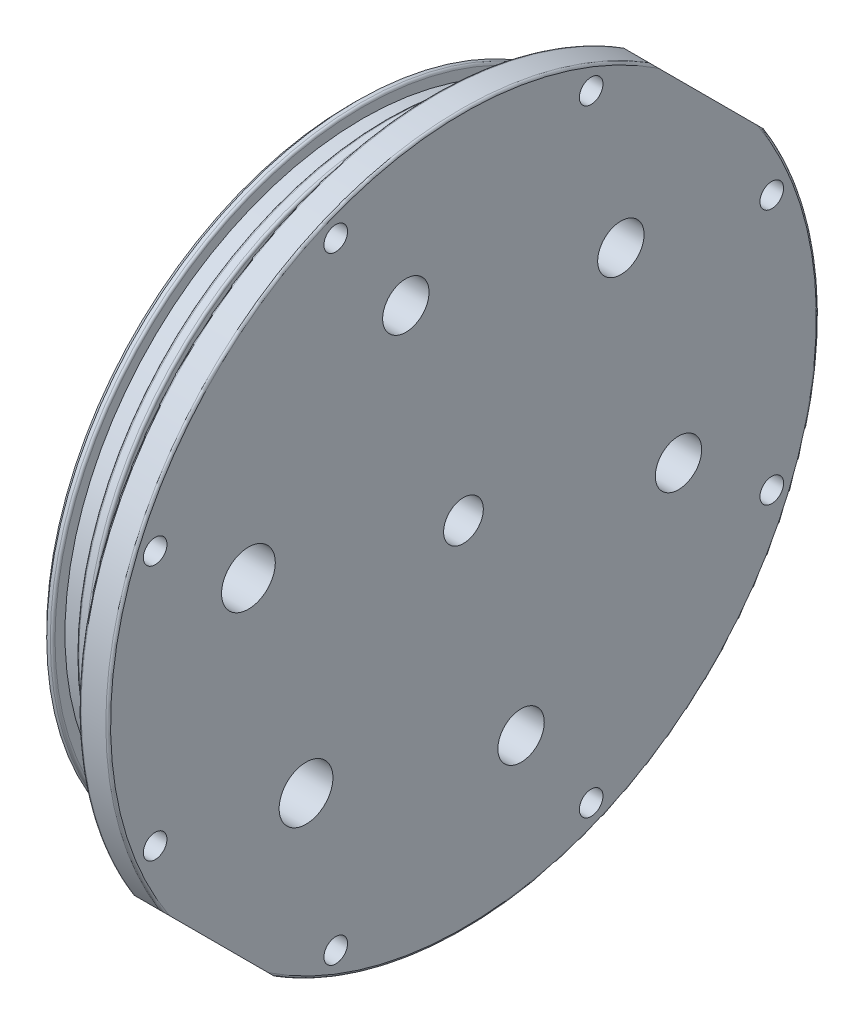
SolidWorks part; units mm, degrees
ref_plane "Front Plane" through (0, 0, 0) normal (0, 0, 1) x (1, 0, 0)
ref_plane "Top Plane" through (0, 0, 0) normal (0, 1, 0) x (1, 0, 0)
ref_plane "Right Plane" through (0, 0, 0) normal (1, 0, 0) x (0, 0, -1)
sketch "Sketch1" plane through (0, 0, 0) normal (0, 0, 1) x (1, 0, 0)
  line L0 (0, 0) -> (0, -58.42) construction
  line L4 (24.13, -58.42) -> (24.13, -76)
  line L5 (24.13, -76) -> (17.8298, -76)
  line L6 (17.8298, -76) -> (17.8298, -66.421)
  line L7 (17.8298, -66.421) -> (0, -66.421) construction
  line L8 (0, -66.294) -> (0, -58.42)
  line L9 (0, -58.42) -> (11.43, -58.42) construction
  line L10 (0, -66.294) -> (2.54, -66.294)
  line L11 (2.54, -66.294) -> (2.54, -63.6575)
  line L12 (2.54, -63.6575) -> (7.6449, -63.6575)
  line L13 (7.6449, -63.6575) -> (7.6449, -66.294)
  line L14 (7.6449, -66.294) -> (10.1849, -66.294)
  line L15 (10.1849, -66.294) -> (10.1849, -63.6575)
  line L16 (10.1849, -63.6575) -> (15.2898, -63.6575)
  line L17 (15.2898, -63.6575) -> (15.2898, -66.294)
  line L18 (15.2898, -66.294) -> (17.8298, -66.294)
  line L19 (17.8298, -66.294) -> (17.8298, -66.421)
  line L20 (0, -66.421) -> (0, -66.294) construction
  line L21 (24.13, -58.42) -> (24.13, 0)
  line L22 (24.13, 0) -> (11.43, 0)
  line L23 (11.43, 0) -> (11.43, -58.42) construction
  line L24 (11.43, -58.42) -> (24.13, -58.42) construction
  line L25 (11.43, 0) -> (0, 0)
  line L26 (0, 0) -> (0, -58.42)
  dimension "CouplerIR" = 58.42
  dimension "CouplerOR" = 76
  dimension "HullR" = 66.421
  dimension "RingSpacing" = 2.54
  dimension "GlandClearanceGap" = 0.254
  dimension "GlandWidth" = 5.1049
  dimension "CouplerHeight" = 24.13
  dimension "BulkheadThickness" = 12.7
  dimension "D1" = 2.7635
revolve "Revolve1" add sketch "Sketch1" angle 360 about L22
chamfer "Chamfer1" distance 1.27 angle 45 1 edges at (0, 66.294, 0)
fillet "Fillet1" radius 0.508 6 edges at (17.8298, 76, 0) (24.13, 76, 0) (15.2898, 66.294, 0) (10.1849, 66.294, 0) (7.6449, 66.294, 0) (2.54, 66.294, 0)
sketch "Sketch4" plane through (24.13, 0, 0) normal (1, 0, 0) x (0, 0, -1)
  line L0 (-65.9527, -27.3185) -> (-27.3185, -65.9527) construction
  line L1 (27.3185, -65.9527) -> (65.9527, -27.3185) construction
  line L2 (65.9527, -27.3185) -> (65.9527, 27.3185) construction
  line L3 (65.9527, 27.3185) -> (27.3185, 65.9527) construction
  line L4 (27.3185, 65.9527) -> (-27.3185, 65.9527) construction
  line L5 (-27.3185, 65.9527) -> (-65.9527, 27.3185) construction
  line L6 (-65.9527, 27.3185) -> (-65.9527, -27.3185) construction
  line L7 (-27.3185, -65.9527) -> (27.3185, -65.9527) construction
  circle A0 centre (0, 0) radius 65.9527 construction
  point P12 (-27.3185, 65.9527)
  point P13 (27.3185, 65.9527)
  point P14 (65.9527, 27.3185)
  point P15 (65.9527, -27.3185)
  point P16 (27.3185, -65.9527)
  point P17 (-27.3185, -65.9527)
  point P18 (-65.9527, -27.3185)
  point P19 (-65.9527, 27.3185)
  dimension "D1" = 142.7734
hole_wizard "#8 (0.199) Diameter Hole1" positions "Sketch4" profile "Sketch5" hole size "#8" standard "ANSI Inch"
sketch "Sketch5" plane through (24.13, 27.3185, 65.9527) normal (0, 1, 0) x (0, 0, -1)
  line L0 (0, 0) -> (0, 10.668)
  line L1 (0, 10.668) -> (2.5273, 9.1494)
  line L2 (2.5273, 9.1494) -> (2.5273, 0)
  line L5 (2.5273, 0) -> (0, 0)
  line L10 (0, 10.668) -> (-2.5273, 9.1494) construction
  line L11 (0, -6.35) -> (0, 107.95) construction
  dimension "Hole Dia." = 5.0546
  dimension "Hole Depth" = 10.668
  dimension "Drill Angle" = 118
sketch "Sketch6" plane through (24.13, 0, 0) normal (1, 0, 0) x (0, 0, -1)
  line L1 (27.3185, 65.9527) -> (65.9527, 27.3185) construction
  line L2 (40.0785, 64.5734) -> (64.5734, 40.0785)
  line L3 (53.7401, 53.7401) -> (72.5758, 34.9044) construction
  line L4 (-53.7401, 53.7401) -> (53.7401, -53.7401) construction
  circle A2 centre (0, 0) radius 76 construction
  arc A3 (64.5734, 40.0785) -> (40.0785, 64.5734) centre (0, 0) ccw
  arc A4 (40.0785, 64.5734) -> (64.5734, 40.0785) centre (0, 0) ccw construction
  dimension "D1" = 2
extrude "Cut-Extrude1" cut sketch "Sketch6" against normal blind 6.35
ref_plane "Plane1" through (0, 0, 0) normal (0, -0.7071, 0.7071) x (0, -0.7071, -0.7071)
sketch "Sketch8" plane through (0, 52.3259, -52.3259) normal (0, 0.7071, -0.7071) x (1, 0, 0)
  line L0 (20.9799, 17.3205) -> (20.9799, 3.937) construction
  line L1 (18.3378, 17.3205) -> (23.622, 17.3205) construction
  line L2 (20.9799, 3.937) -> (20.9799, -3.937) construction
  line L3 (20.9799, -3.937) -> (20.9799, -17.3205) construction
  line L4 (18.3378, -17.3205) -> (23.622, -17.3205) construction
  point P9 (20.9799, 3.937)
  point P10 (20.9799, -3.937)
  dimension "D1" = 7.874
hole_wizard "#6-32 Tapped Hole1" positions "3DSketch1" profile "Sketch9" tap size "#6-32" standard "ANSI Inch"
sketch3d "3DSketch1"
  point P0 (20.9799, 49.542, -55.1098)
  point P3 (20.9799, 55.1098, -49.542)
sketch "Sketch9" plane through (20.9799, 49.542, -55.1098) normal (1, 0, 0) x (0, 0.7071, 0.7071)
  line L0 (0, 0) -> (0, 19.05)
  line L1 (0, 19.05) -> (1.3525, 18.2373)
  line L2 (1.3525, 18.2373) -> (1.3525, 0)
  line L5 (1.3525, 0) -> (0, 0)
  line L10 (0, 19.05) -> (-1.3526, 18.2373) construction
  line L11 (0, -6.35) -> (0, 107.95) construction
  dimension "Tap Drill Dia." = 2.7051
  dimension "Tap Drill Depth" = 19.05
  dimension "Drill Angle" = 118
cosmetic thread "Hole Thread7" parameters "D1"=7.112, "D2"=3.5052
cosmetic thread "Hole Thread8" parameters "D1"=7.112, "D2"=3.5052
mirror "Mirror1" about plane through (0, 0, 0) normal (0, -0.7071, 0.7071) of "#6-32 Tapped Hole1", "Cut-Extrude1"
cosmetic thread "Hole Thread9" parameters "D1"=7.112, "D2"=3.5052
cosmetic thread "Hole Thread10" parameters "D1"=7.112, "D2"=3.5052
sketch "Sketch11" plane through (24.13, 0, 0) normal (1, 0, 0) x (0, 0, -1)
  point P0 (0, 0)
hole_wizard "M10x1.5 Tapped Hole1" positions "Sketch11" profile "Sketch12" tap size "M10x1.5" standard "ANSI Metric"
sketch "Sketch12" plane through (24.13, 0, 0) normal (0, 1, 0) x (0, 0, -1)
  line L0 (0, 0) -> (0, 30.48)
  line L1 (0, 30.48) -> (4.25, 27.9263)
  line L2 (4.25, 27.9263) -> (4.25, 0)
  line L5 (4.25, 0) -> (0, 0)
  line L10 (0, 30.48) -> (-4.25, 27.9263) construction
  line L11 (0, -6.35) -> (0, 107.95) construction
  dimension "Tap Drill Dia." = 8.5
  dimension "Tap Drill Depth" = 30.48
  dimension "Drill Angle" = 118
cosmetic thread "Hole Thread11" parameters "D1"=20.066, "D2"=10
sketch "Sketch2" plane through (24.13, 0, 0) normal (1, 0, 0) x (0, 0, -1)
  line L1 (12.3263, -46.0022) -> (46.0022, -12.3263) construction
  line L2 (46.0022, -12.3263) -> (33.676, 33.676) construction
  line L3 (33.676, 33.676) -> (-12.3263, 46.0022) construction
  line L4 (-12.3263, 46.0022) -> (-46.0022, 12.3263) construction
  line L5 (-46.0022, 12.3263) -> (-33.676, -33.676) construction
  line L6 (-33.676, -33.676) -> (12.3263, -46.0022) construction
  line L8 (-52.3259, -52.3259) -> (52.3259, 52.3259) construction
  line L9 (-62.8863, -41.7655) -> (-41.7655, -62.8863) construction
  line L10 (55.1098, 49.542) -> (49.542, 55.1098) construction
  circle A0 centre (0, 0) radius 41.2445 construction
  point P10 (-12.3263, 46.0022)
  point P13 (33.676, 33.676)
  point P14 (46.0022, -12.3263)
  point P15 (12.3263, -46.0022)
  dimension "D1" = 47.625
hole_wizard "7/16-20 Tapped Hole1" positions "Sketch2" profile "Sketch3" tap size "7/16-20" standard "ANSI Inch"
sketch "Sketch3" plane through (24.13, -46.0022, -12.3263) normal (0, 1, 0) x (0, 0, -1)
  line L0 (0, 0) -> (0, 30.48)
  line L1 (0, 30.48) -> (4.9606, 27.4994)
  line L2 (4.9606, 27.4994) -> (4.9606, 0)
  line L5 (4.9606, 0) -> (0, 0)
  line L10 (0, 30.48) -> (-4.9606, 27.4994) construction
  line L11 (0, -6.35) -> (0, 107.95) construction
  dimension "Tap Drill Dia." = 9.9212
  dimension "Tap Drill Depth" = 30.48
  dimension "Drill Angle" = 118
cosmetic thread "Hole Thread1" parameters "D1"=22.352, "D2"=11.1125
cosmetic thread "Hole Thread2" parameters "D1"=22.352, "D2"=11.1125
cosmetic thread "Hole Thread3" parameters "D1"=22.352, "D2"=11.1125
cosmetic thread "Hole Thread6" parameters "D1"=22.352, "D2"=11.1125
sketch "Sketch14" plane through (24.13, 0, 0) normal (1, 0, 0) x (0, 0, -1)
  point P0 (-46.0022, 12.3263)
  point P1 (-33.676, -33.676)
hole_wizard "1/2-20 Tapped Hole1" positions "Sketch14" profile "Sketch15" tap size "1/2-20" standard "ANSI Inch"
sketch "Sketch15" plane through (24.13, 12.3263, 46.0022) normal (0, 1, 0) x (0, 0, -1)
  line L0 (0, 0) -> (0, 29.21)
  line L1 (0, 29.21) -> (5.7544, 25.7524)
  line L2 (5.7544, 25.7524) -> (5.7544, 0)
  line L5 (5.7544, 0) -> (0, 0)
  line L10 (0, 29.21) -> (-5.7544, 25.7524) construction
  line L11 (0, -6.35) -> (0, 107.95) construction
  dimension "Tap Drill Dia." = 11.5087
  dimension "Tap Drill Depth" = 29.21
  dimension "Drill Angle" = 118
cosmetic thread "Hole Thread12" parameters "D1"=25.4, "D2"=12.7
cosmetic thread "Hole Thread13" parameters "D1"=25.4, "D2"=12.7
sketch "Sketch17" plane through (0, 0, 0) normal (-1, 0, 0) x (0, 0, 1)
  line L1 (-27.2199, -27.2199) -> (9.9632, -37.1831) construction
  line L2 (9.9632, -37.1831) -> (37.1831, -9.9632) construction
  line L3 (37.1831, -9.9632) -> (27.2199, 27.2199) construction
  line L4 (27.2199, 27.2199) -> (-9.9632, 37.1831) construction
  line L5 (-9.9632, 37.1831) -> (-37.1831, 9.9632) construction
  line L6 (-37.1831, 9.9632) -> (-27.2199, -27.2199) construction
  line L7 (12.3263, 46.0022) -> (46.0022, 12.3263) construction
  circle A0 centre (0, 0) radius 33.3375 construction
  point P10 (27.2199, 27.2199)
  point P11 (37.1831, -9.9632)
  point P12 (9.9632, -37.1831)
  point P13 (-27.2199, -27.2199)
  point P14 (-37.1831, 9.9632)
  point P15 (-9.9632, 37.1831)
  dimension "D1" = 38.4948
hole_wizard "#8-32 Tapped Hole1" positions "Sketch17" profile "Sketch18" tap size "#8-32" standard "ANSI Inch"
sketch "Sketch18" plane through (0, 37.1831, -9.9632) normal (0, 1, 0) x (0, 0, 1)
  line L0 (0, 0) -> (0, 10.7594)
  line L1 (0, 10.7594) -> (1.7272, 9.7216)
  line L2 (1.7272, 9.7216) -> (1.7272, 0)
  line L5 (1.7272, 0) -> (0, 0)
  line L10 (0, 10.7594) -> (-1.7272, 9.7216) construction
  line L11 (0, -6.35) -> (0, 107.95) construction
  dimension "Tap Drill Dia." = 3.4544
  dimension "Tap Drill Depth" = 10.7594
  dimension "Drill Angle" = 118
cosmetic thread "Hole Thread14" parameters "D1"=8.382, "D2"=4.1656
cosmetic thread "Hole Thread15" parameters "D1"=8.382, "D2"=4.1656
cosmetic thread "Hole Thread16" parameters "D1"=8.382, "D2"=4.1656
cosmetic thread "Hole Thread17" parameters "D1"=8.382, "D2"=4.1656
cosmetic thread "Hole Thread18" parameters "D1"=8.382, "D2"=4.1656
cosmetic thread "Hole Thread19" parameters "D1"=8.382, "D2"=4.1656
equation "\"HullID\"= 5.230"
equation "\"HullIR\"= \"HullID\" / 2"
equation "\"CrossSectionThickness\"= .136"
equation "\"RingCompression\"= .2"
equation "\"GlandDepth\"= \"CrossSectionThickness\" * ( 1 - \"RingCompression\" )"
equation "\"D1@Sketch1\"=\"GlandDepth\""
equation "\"RingCSArea\"= .0164"
equation "\"GlandFill\"= .75"
equation "\"GlandWidth\"= 1 / \"GlandFill\" * \"RingCSArea\" / \"GlandDepth\""
equation "\"GlandWidth@Sketch1\"= \"GlandWidth\""
